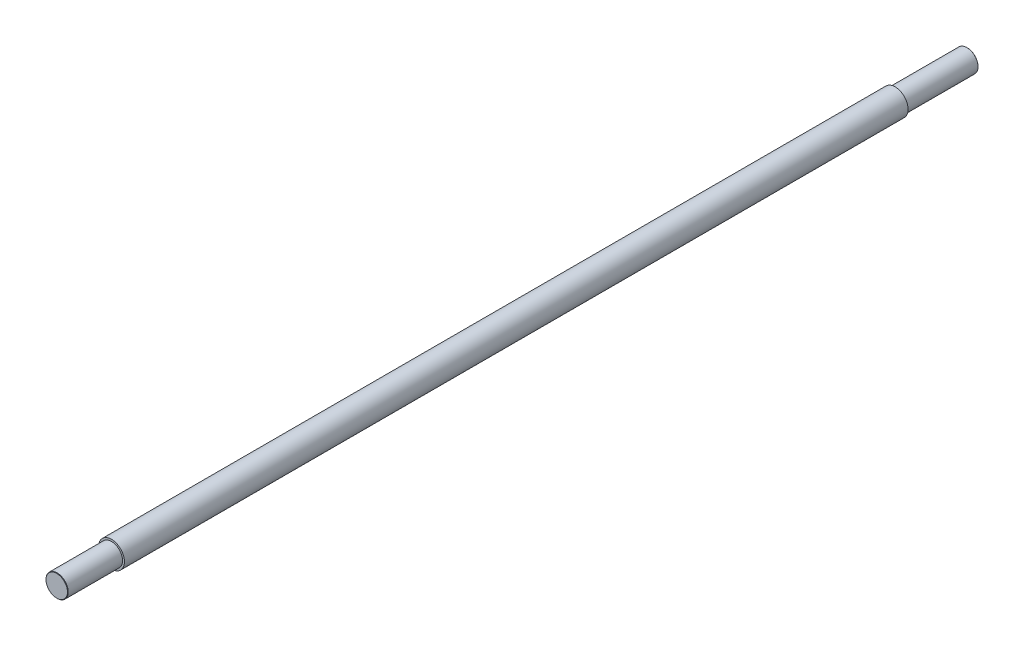
SolidWorks part; units mm, degrees
material "AISI 1045 钢，冷拔"
ref_plane "前视基准面" through (0, 0, 0) normal (0, 0, 1) x (1, 0, 0)
ref_plane "上视基准面" through (0, 0, 0) normal (0, 1, 0) x (1, 0, 0)
ref_plane "右视基准面" through (0, 0, 0) normal (1, 0, 0) x (0, 0, -1)
sketch "草图1" plane through (0, 0, 0) normal (1, 0, 0) x (0, 0, -1)
  line L0 (0, 0) -> (2461, 0) construction
  line L1 (0, 0) -> (0, 30)
  line L2 (0, 30) -> (148, 30)
  line L3 (148, 30) -> (148, 35)
  line L4 (148, 35) -> (2266, 35)
  line L5 (2266, 35) -> (2266, 30)
  line L6 (2266, 30) -> (2461, 30)
  line L7 (2461, 30) -> (2461, 0)
  line L8 (2461, 0) -> (0, 0)
  dimension "D1" = 2461
  dimension "D2" = 30
  dimension "D3" = 35
  dimension "D4" = 30
  dimension "D5" = 148
  dimension "D6" = 195
revolve "旋转1" add sketch "草图1" angle 360 about L0
chamfer "倒角1" distance 1 angle 45 1 edges at (0, -30, -2461)
chamfer "倒角2" distance 1 angle 45 1 edges at (0, -30, 0)
